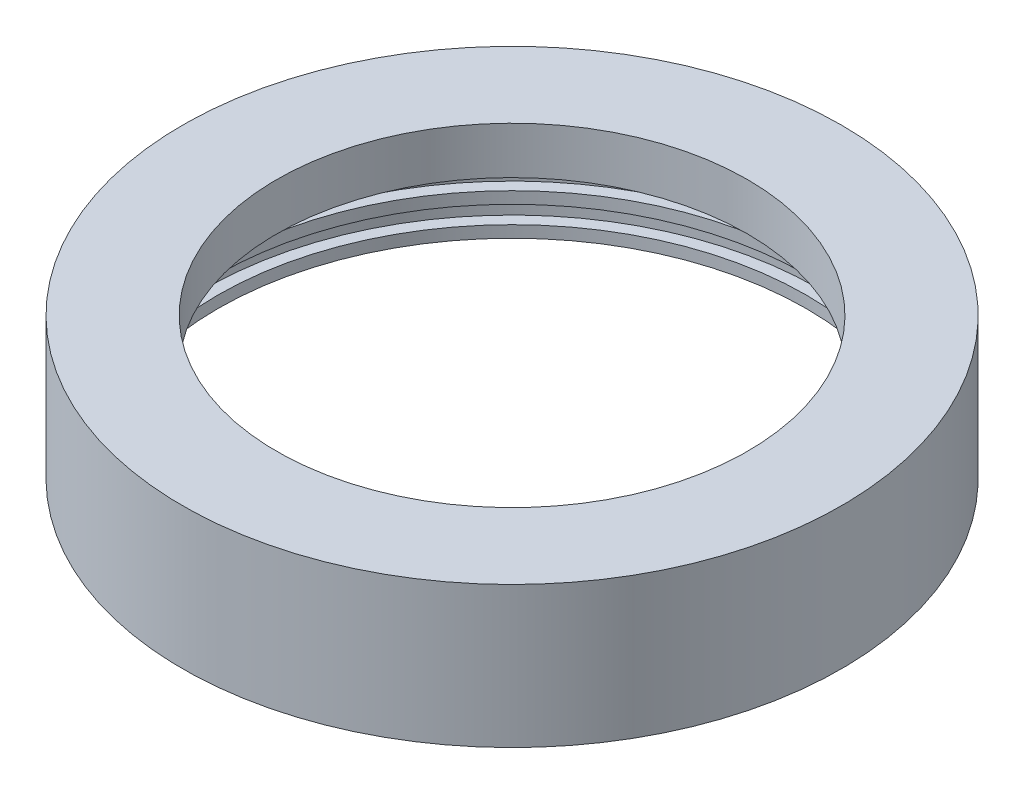
SolidWorks part; units mm, degrees
material "6061 Alloy"
ref_plane "Front Plane" through (0, 0, 0) normal (0, 0, 1) x (1, 0, 0)
ref_plane "Top Plane" through (0, 0, 0) normal (0, 1, 0) x (1, 0, 0)
ref_plane "Right Plane" through (0, 0, 0) normal (1, 0, 0) x (0, 0, -1)
sketch "Sketch1" plane through (0, 0, 0) normal (0, 0, 1) x (1, 0, 0)
  line L14 (63.5, 25.4) -> (79.375, 25.4)
  line L15 (79.375, 25.4) -> (79.375, 15.875)
  line L16 (79.375, 15.875) -> (82.55, 15.875)
  line L17 (82.55, 15.875) -> (82.55, 11.1125)
  line L18 (82.55, 11.1125) -> (79.375, 11.1125)
  line L19 (79.375, 11.1125) -> (79.375, 7.9375)
  line L20 (79.375, 7.9375) -> (82.55, 7.9375)
  line L21 (82.55, 7.9375) -> (82.55, 3.175)
  line L22 (82.55, 3.175) -> (79.375, 3.175)
  line L23 (79.375, 3.175) -> (79.375, 0)
  line L24 (79.375, 0) -> (88.9, 0)
  line L25 (88.9, 0) -> (88.9, 38.1)
  line L34 (63.5, 25.4) -> (63.5, 38.1)
  line L35 (63.5, 38.1) -> (88.9, 38.1)
  line L36 (0, 0) -> (0, 28.4075) construction
  point P2 (0, 0)
  dimension "D1" = 88.9
  dimension "D2" = 15.875
  dimension "D3" = 3.175
  dimension "D4" = 3.175
  dimension "D5" = 4.7625
  dimension "D6" = 12.7
  dimension "D7" = 38.1
  dimension "D9" = 9.525
revolve "Revolve1" add sketch "Sketch1" angle 360 about L36
